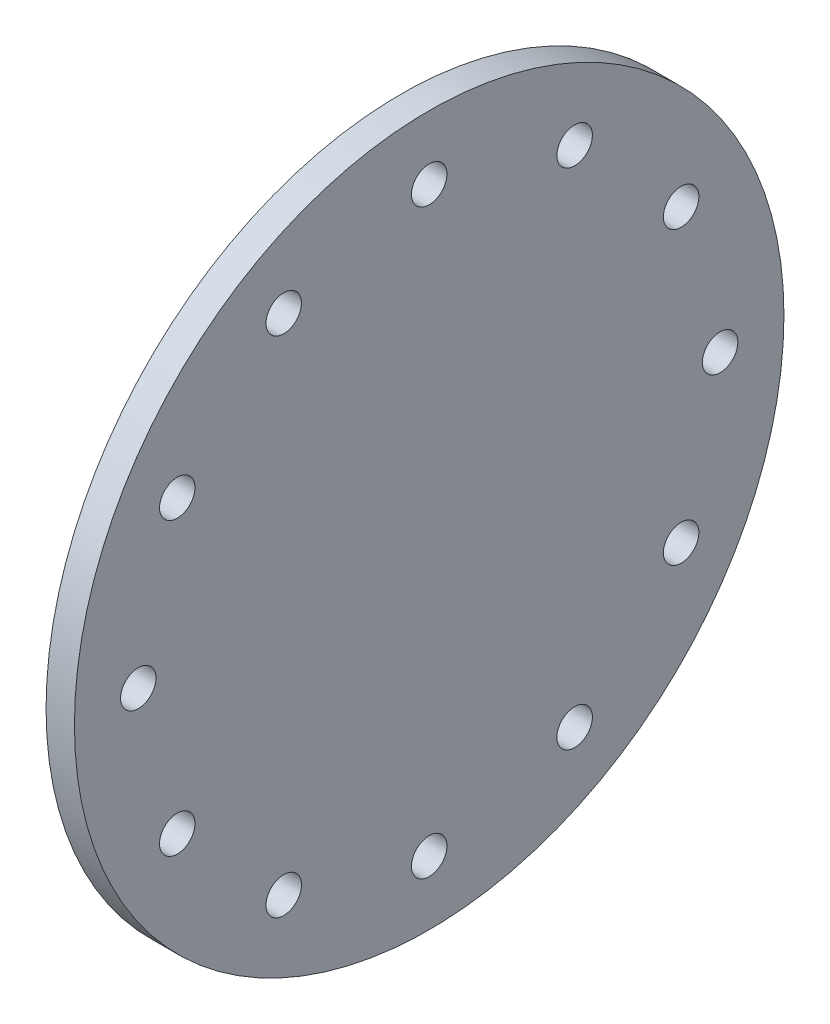
SolidWorks part; units mm, degrees
ref_plane "Front Plane" through (0, 0, 0) normal (0, 0, 1) x (1, 0, 0)
ref_plane "Top Plane" through (0, 0, 0) normal (0, 1, 0) x (1, 0, 0)
ref_plane "Right Plane" through (0, 0, 0) normal (1, 0, 0) x (0, 0, -1)
sketch "Sketch1" plane through (0, 0, 0) normal (1, 0, 0) x (0, 0, -1)
  circle A0 centre (0, 0) radius 2500
  circle A1 centre (0, 0) radius 2050 construction
  circle A2 centre (0, 2050) radius 125
  circle A3 centre (1025, 1775.3521) radius 125
  circle A4 centre (1775.3521, 1025) radius 125
  circle A5 centre (2050, 0) radius 125
  circle A6 centre (1775.3521, -1025) radius 125
  circle A7 centre (1025, -1775.3521) radius 125
  circle A8 centre (0, -2050) radius 125
  circle A9 centre (-1025, -1775.3521) radius 125
  circle A10 centre (-1775.3521, -1025) radius 125
  circle A11 centre (-2050, 0) radius 125
  circle A12 centre (-1775.3521, 1025) radius 125
  circle A13 centre (-1025, 1775.3521) radius 125
  point P30 (0, 0)
  dimension "D1" = 5000
  dimension "D2" = 4100
  dimension "D3" = 250
  dimension "D4" = 12
extrude "Boss-Extrude1" add sketch "Sketch1" along normal blind 200 contours A11 | A10 | A9 | A8 | A6 | A7 | A5 | A4 | A3 | A2 | A13 | A0 | A12
